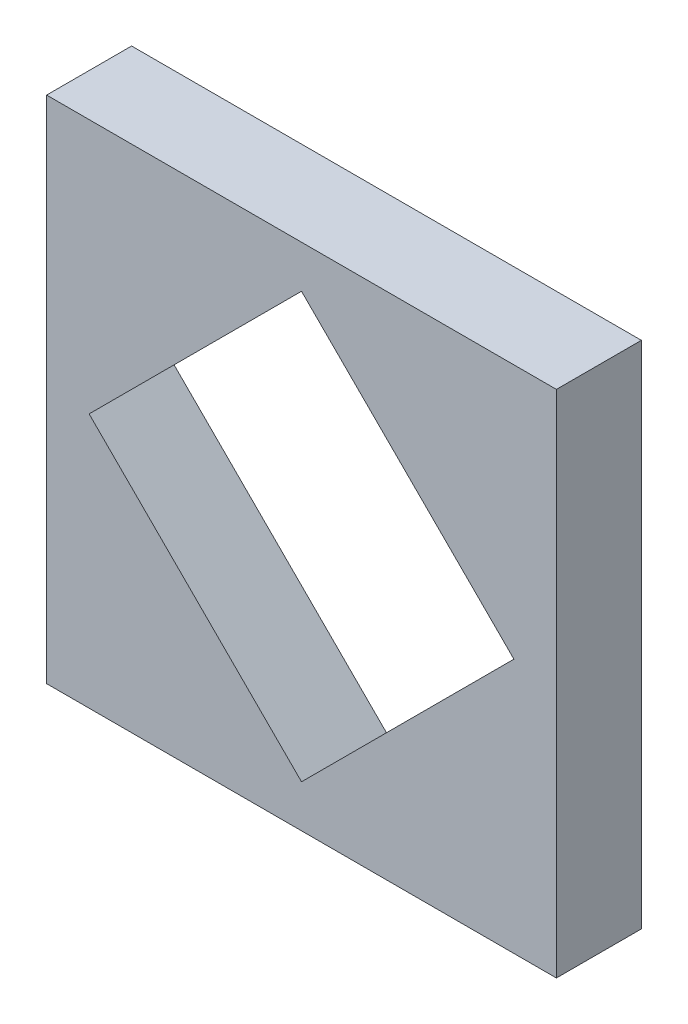
SolidWorks part; units mm, degrees
ref_plane "Piano frontale" through (0, 0, 0) normal (0, 0, 1) x (1, 0, 0)
ref_plane "Piano superiore" through (0, 0, 0) normal (0, 1, 0) x (1, 0, 0)
ref_plane "Piano destro" through (0, 0, 0) normal (1, 0, 0) x (0, 0, -1)
sketch "Schizzo1" plane through (0, 0, 0) normal (0, 0, 1) x (1, 0, 0)
  line L0 (0, -25) -> (25, 0)
  line L1 (-30, 30) -> (30, 30)
  line L2 (-30, 30) -> (-30, -30)
  line L3 (-30, -30) -> (30, -30)
  line L4 (30, 30) -> (30, -30)
  line L5 (25, 0) -> (0, 25)
  line L6 (0, 25) -> (-25, 0)
  line L7 (-25, 0) -> (0, -25)
  circle A0 centre (0, 0) radius 25 construction
  dimension "D1" = 60
  dimension "D2" = 60
  dimension "D3" = 30
extrude "Estrusione-Estrusione1" add sketch "Schizzo1" along normal blind 10 contours L5 L6 L7 L0 | L1 L4 L3 L2
